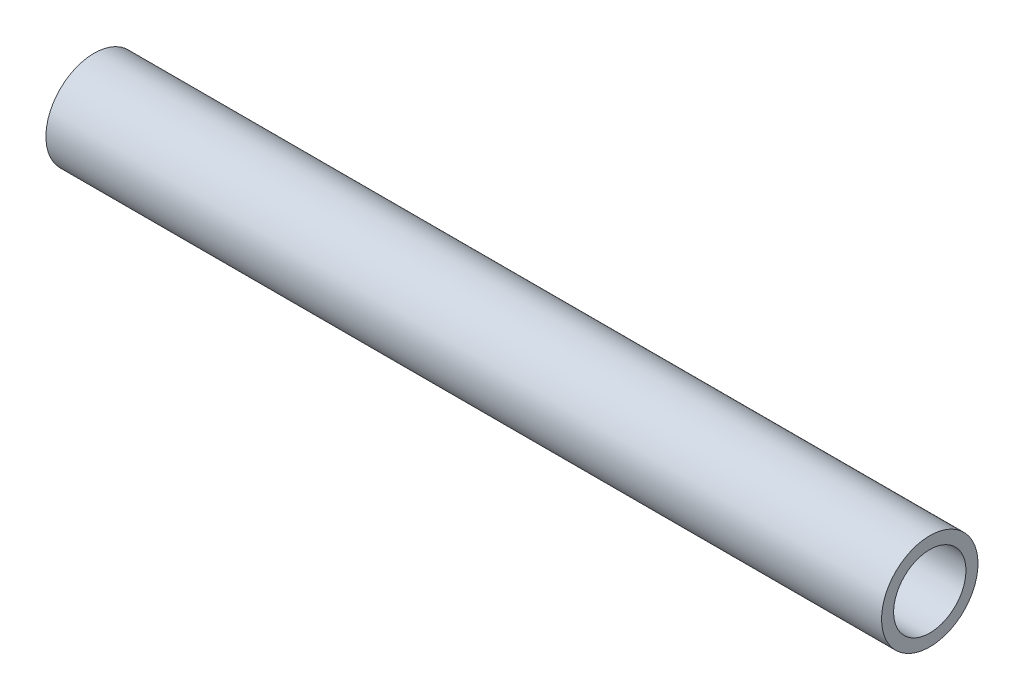
SolidWorks part; units mm, degrees
ref_plane "Front Plane" through (0, 0, 0) normal (0, 0, 1) x (1, 0, 0)
ref_plane "Top Plane" through (0, 0, 0) normal (0, 1, 0) x (1, 0, 0)
ref_plane "Right Plane" through (0, 0, 0) normal (1, 0, 0) x (0, 0, -1)
sketch "Sketch1" plane through (0, 0, 0) normal (1, 0, 0) x (0, 0, -1)
  circle A0 centre (0, 0) radius 2.25
  circle A1 centre (0, 0) radius 3
  dimension "D1" = 4.5
  dimension "D2" = 6
extrude "Boss-Extrude1" add sketch "Sketch1" along normal mid plane 52
